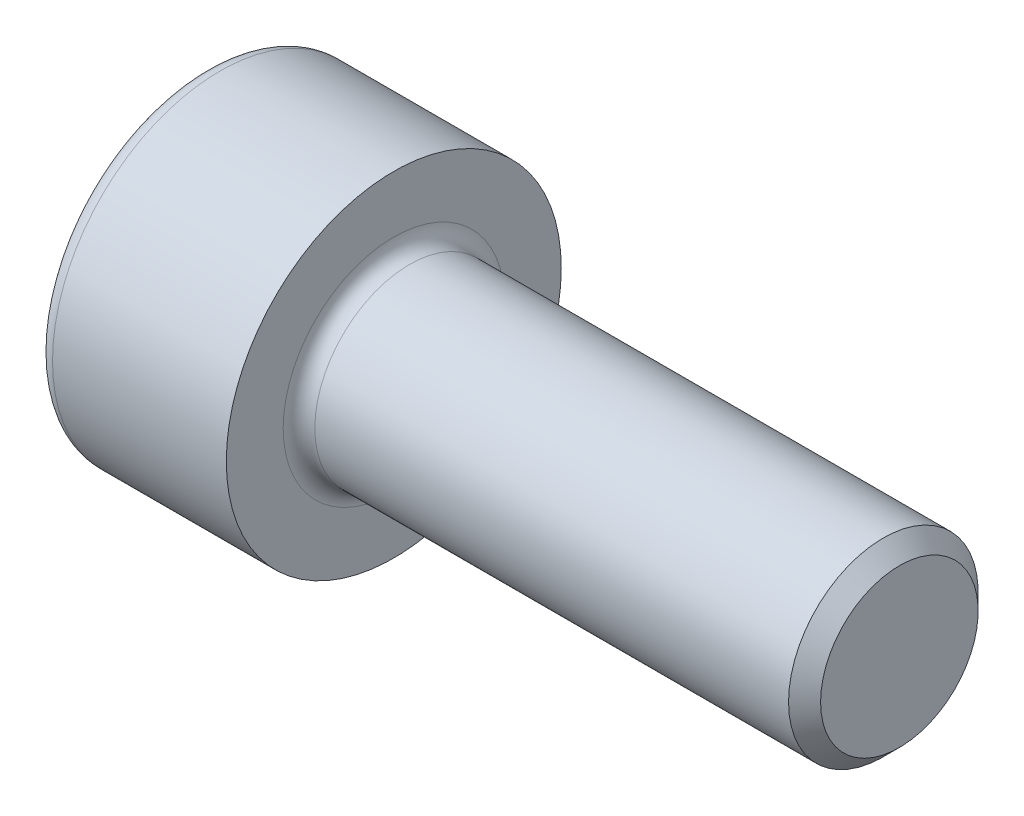
SolidWorks part; units mm, degrees
ref_plane "Front" through (0, 0, 0) normal (0, 0, 1) x (1, 0, 0)
ref_plane "Top" through (0, 0, 0) normal (0, 1, 0) x (1, 0, 0)
ref_plane "Right" through (0, 0, 0) normal (1, 0, 0) x (0, 0, -1)
sketch "Sketch1" plane through (0, 0, 0) normal (0, 0, 1) x (1, 0, 0)
  line L0 (7.7465, 1.5) -> (0.25, 1.5)
  line L1 (-3, 2.4) -> (-3, 0)
  line L2 (0, 2.65) -> (-2.75, 2.65)
  line L3 (0, 1.75) -> (0, 2.65)
  line L4 (8, 1.2465) -> (8, 0)
  line L5 (8, 1.2465) -> (7.7465, 1.5)
  line L6 (-3, 0) -> (0, 0) construction
  line L7 (-3, 0) -> (8, 0)
  arc A0 (-2.75, 2.65) -> (-3, 2.4) centre (-2.75, 2.4) ccw
  arc A1 (0, 1.75) -> (0.25, 1.5) centre (0.25, 1.75) ccw
  point P12 (0, 2.2)
  dimension "D5" = 0.25
  dimension "D1" = 3
  dimension "D2" = 5.3
  dimension "D3" = 135
  dimension "D4" = 0.3585
  dimension "D6" = 8
  dimension "D7" = 3
revolve "Revolve1" add sketch "Sketch1" angle 360 about L7
sketch "Sketch2" plane through (-3, 0, 0) normal (-1, 0, 0) x (0, 0, 1)
  line L7 (1.25, 0.7217) -> (0, 1.4434)
  line L8 (0, 1.4434) -> (-1.25, 0.7217)
  line L9 (-1.25, 0.7217) -> (-1.25, -0.7217)
  line L10 (-1.25, -0.7217) -> (0, -1.4434)
  line L11 (0, -1.4434) -> (1.25, -0.7217)
  line L12 (1.25, -0.7217) -> (1.25, 0.7217)
  circle A0 centre (0, 0) radius 1.25 construction
  dimension "D1" = 2.5
extrude "Cut-Extrude1" cut sketch "Sketch2" against normal blind 1.1
